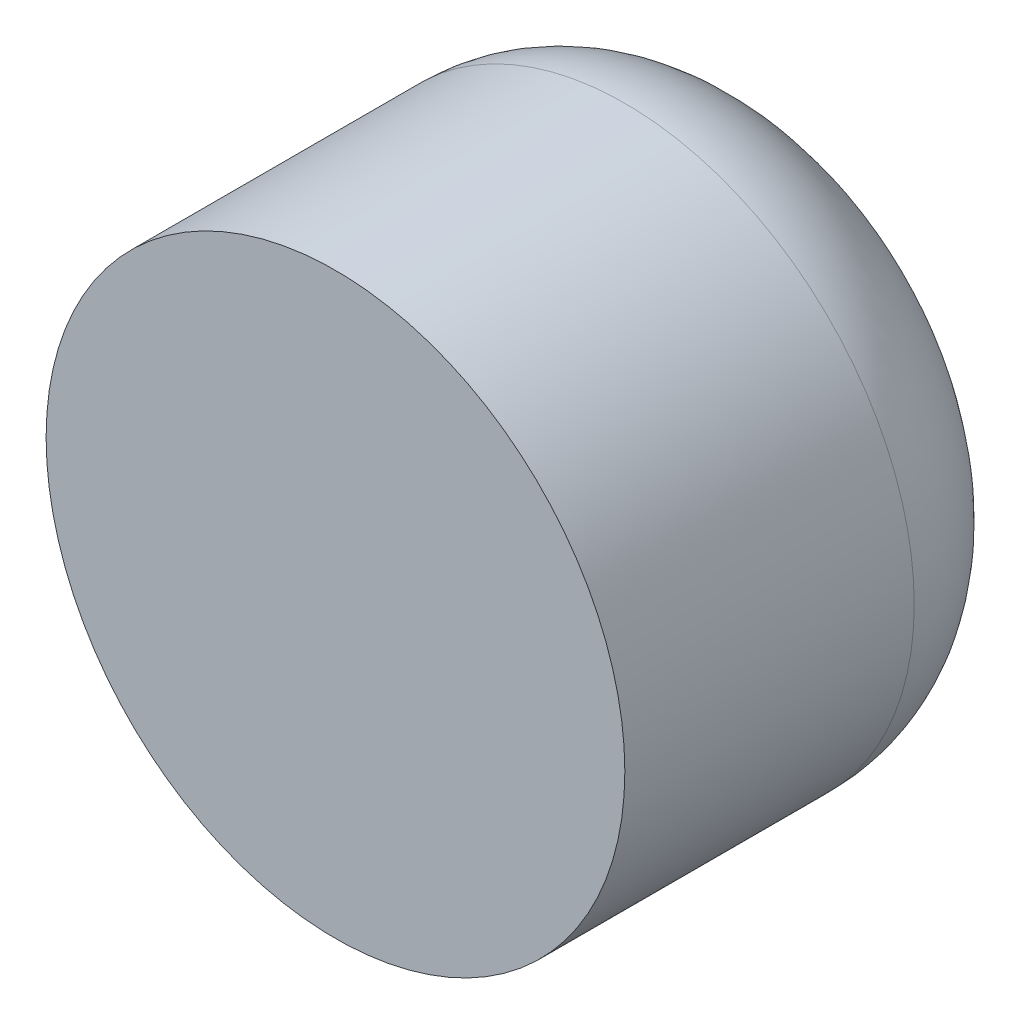
SolidWorks part; units mm, degrees
ref_plane "Front Plane" through (0, 0, 0) normal (0, 0, 1) x (1, 0, 0)
ref_plane "Top Plane" through (0, 0, 0) normal (0, 1, 0) x (1, 0, 0)
ref_plane "Right Plane" through (0, 0, 0) normal (1, 0, 0) x (0, 0, -1)
sketch "Sketch1" plane through (0, 0, 0) normal (0, 0, 1) x (1, 0, 0)
  circle A0 centre (-4.5746, 1.3364) radius 2
  dimension "D1" = 4
extrude "Boss-Extrude2" add sketch "Sketch1" along normal blind 3 contours A0
sketch "Sketch2" plane through (0, 0, 0) normal (0, 0, -1) x (-1, 0, 0)
  line L1 (4.1106, 2.1308) -> (3.6546, 1.3317)
  line L2 (3.6546, 1.3317) -> (4.1187, 0.5373)
  line L3 (4.1187, 0.5373) -> (5.0387, 0.542)
  line L4 (5.0387, 0.542) -> (5.4947, 1.3411)
  line L5 (5.4947, 1.3411) -> (5.0306, 2.1355)
  line L6 (5.0306, 2.1355) -> (4.1106, 2.1308)
  circle A0 centre (4.5746, 1.3364) radius 0.7968 construction
extrude "Cut-Extrude1" cut sketch "Sketch2" against normal blind 2
fillet "Fillet5" radius 1 1 edges at (-2.5746, 1.3364, 0)
